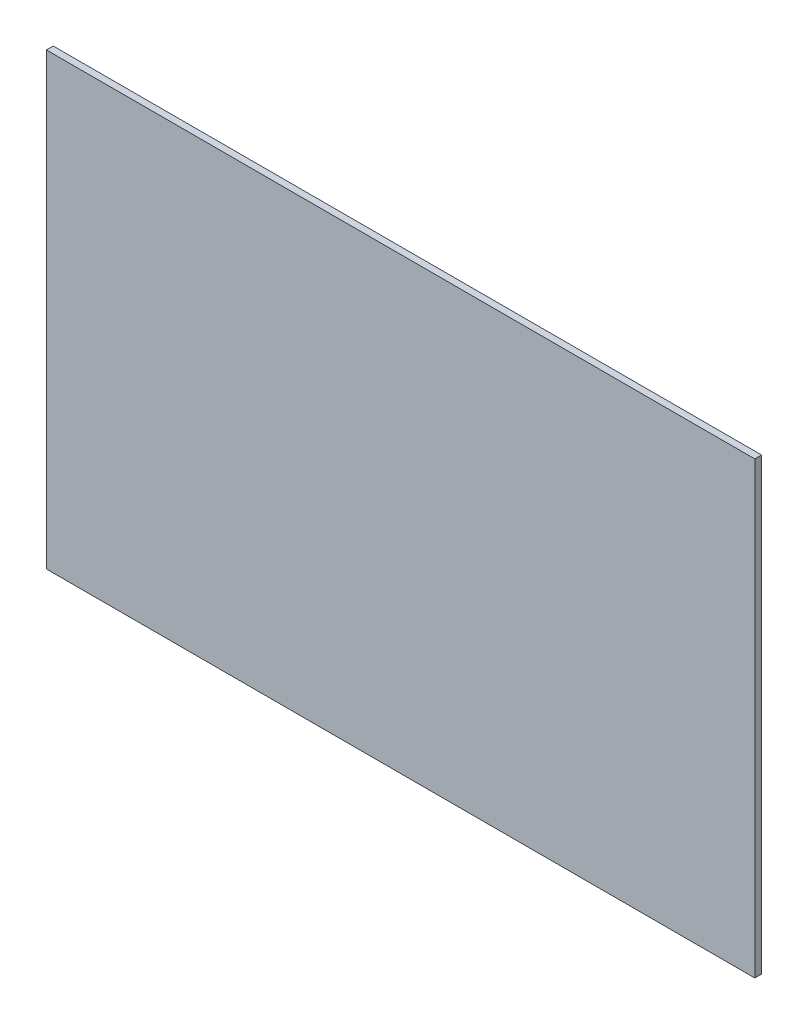
SolidWorks part; units mm, degrees
ref_plane "Plan de face" through (0, 0, 0) normal (0, 0, 1) x (1, 0, 0)
ref_plane "Plan de dessus" through (0, 0, 0) normal (0, 1, 0) x (1, 0, 0)
ref_plane "Plan de droite" through (0, 0, 0) normal (1, 0, 0) x (0, 0, -1)
sketch "Esquisse1" plane through (0, 0, 0) normal (0, 0, 1) x (1, 0, 0)
  line L1 (-207.9898, 236.4612) -> (312.0102, 236.4612)
  line L2 (-207.9898, 236.4612) -> (-207.9898, -93.5388)
  line L3 (-207.9898, -93.5388) -> (312.0102, -93.5388)
  line L4 (312.0102, 236.4612) -> (312.0102, -93.5388)
  dimension "D1" = 520
  dimension "D2" = 330
extrude "Boss.-Extru.1" add sketch "Esquisse1" along normal blind 5
